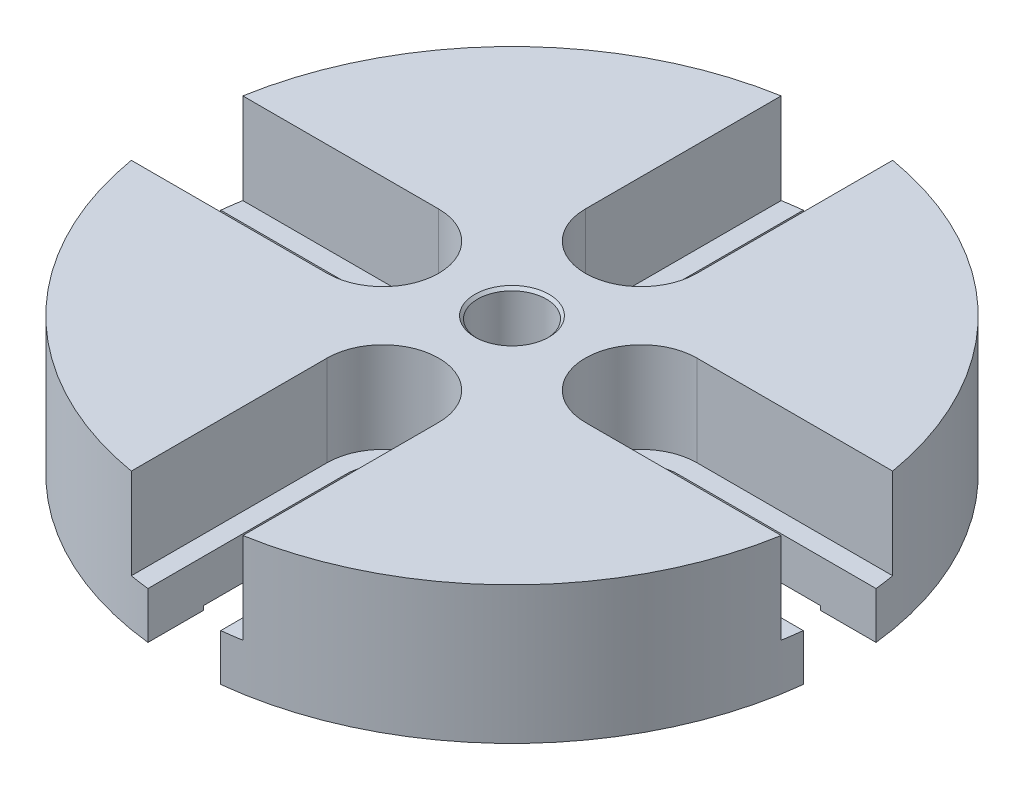
SolidWorks part; units mm, degrees
ref_plane "Front Plane" through (0, 0, 0) normal (0, 0, 1) x (1, 0, 0)
ref_plane "Top Plane" through (0, 0, 0) normal (0, 1, 0) x (1, 0, 0)
ref_plane "Right Plane" through (0, 0, 0) normal (1, 0, 0) x (0, 0, -1)
ref_plane "Plane1" through (0, 0, 0) normal (0, 0, -1) x (-1, 0, 0)
sketch "Sketch1" plane through (0, 0, 0) normal (0, 0, -1) x (-1, 0, 0)
  line L0 (-30.48, -6.35) -> (0, -6.35)
  line L1 (0, -6.35) -> (0, 6.35)
  line L2 (0, 6.35) -> (-30.48, 6.35)
  line L3 (-30.48, 6.35) -> (-30.48, -6.35)
  line L4 (0, -6.35) -> (0, 6.35) construction
revolve "Revolve1" add sketch "Sketch1" angle 360 about L4
sketch "Sketch2" plane through (0, 6.35, 0) normal (0, 1, 0) x (-1, 0, 0)
  line L0 (5.1562, -30.0407) -> (5.1562, -11.938)
  line L1 (-5.1562, -11.938) -> (-5.1562, -30.0407)
  arc A0 (5.1562, -11.938) -> (-5.1562, -11.938) centre (0, -11.938) ccw
  arc A1 (-5.1562, -30.0407) -> (5.1562, -30.0407) centre (0, 0) ccw
extrude "Cut-Extrude1" cut sketch "Sketch2" against normal blind 8.382
sketch "Sketch3" plane through (0, -2.032, 0) normal (0, 1, 0) x (-1, 0, 0)
  line L0 (3.3655, -30.2936) -> (3.3655, -11.938)
  line L1 (-3.3655, -11.938) -> (-3.3655, -30.2936)
  arc A0 (3.3655, -11.938) -> (-3.3655, -11.938) centre (0, -11.938) ccw
  arc A1 (-3.3655, -30.2936) -> (3.3655, -30.2936) centre (0, 0) ccw
extrude "Cut-Extrude2" cut sketch "Sketch3" against normal through all
sketch "Sketch4" plane through (0, 6.35, 0) normal (0, 1, 0) x (-1, 0, 0)
  line L0 (-30.0407, -5.1562) -> (-11.938, -5.1562)
  line L1 (-11.938, 5.1562) -> (-30.0407, 5.1562)
  arc A0 (-11.938, -5.1562) -> (-11.938, 5.1562) centre (-11.938, 0) ccw
  arc A1 (-30.0407, 5.1562) -> (-30.0407, -5.1562) centre (0, 0) ccw
extrude "Cut-Extrude3" cut sketch "Sketch4" against normal blind 8.382
sketch "Sketch5" plane through (0, -2.032, 0) normal (0, 1, 0) x (-1, 0, 0)
  line L0 (-30.2936, -3.3655) -> (-11.938, -3.3655)
  line L1 (-11.938, 3.3655) -> (-30.2936, 3.3655)
  arc A0 (-11.938, -3.3655) -> (-11.938, 3.3655) centre (-11.938, 0) ccw
  arc A1 (-30.2936, 3.3655) -> (-30.2936, -3.3655) centre (0, 0) ccw
extrude "Cut-Extrude4" cut sketch "Sketch5" against normal through all
sketch "Sketch6" plane through (0, 6.35, 0) normal (0, 1, 0) x (-1, 0, 0)
  line L0 (-5.1562, 30.0407) -> (-5.1562, 11.938)
  line L1 (5.1562, 11.938) -> (5.1562, 30.0407)
  arc A0 (-5.1562, 11.938) -> (5.1562, 11.938) centre (0, 11.938) ccw
  arc A1 (5.1562, 30.0407) -> (-5.1562, 30.0407) centre (0, 0) ccw
extrude "Cut-Extrude5" cut sketch "Sketch6" against normal blind 8.382
sketch "Sketch7" plane through (0, -2.032, 0) normal (0, 1, 0) x (-1, 0, 0)
  line L0 (-3.3655, 30.2936) -> (-3.3655, 11.938)
  line L1 (3.3655, 11.938) -> (3.3655, 30.2936)
  arc A0 (-3.3655, 11.938) -> (3.3655, 11.938) centre (0, 11.938) ccw
  arc A1 (3.3655, 30.2936) -> (-3.3655, 30.2936) centre (0, 0) ccw
extrude "Cut-Extrude6" cut sketch "Sketch7" against normal through all
sketch "Sketch8" plane through (0, 6.35, 0) normal (0, 1, 0) x (-1, 0, 0)
  line L0 (30.0407, 5.1562) -> (11.938, 5.1562)
  line L1 (11.938, -5.1562) -> (30.0407, -5.1562)
  arc A0 (11.938, 5.1562) -> (11.938, -5.1562) centre (11.938, 0) ccw
  arc A1 (30.0407, -5.1562) -> (30.0407, 5.1562) centre (0, 0) ccw
extrude "Cut-Extrude7" cut sketch "Sketch8" against normal blind 8.382
sketch "Sketch9" plane through (0, -2.032, 0) normal (0, 1, 0) x (-1, 0, 0)
  line L0 (30.2936, 3.3655) -> (11.938, 3.3655)
  line L1 (11.938, -3.3655) -> (30.2936, -3.3655)
  arc A0 (11.938, 3.3655) -> (11.938, -3.3655) centre (11.938, 0) ccw
  arc A1 (30.2936, -3.3655) -> (30.2936, 3.3655) centre (0, 0) ccw
extrude "Cut-Extrude8" cut sketch "Sketch9" against normal through all
hole_wizard "Hole1" positions "Sketch11" profile "Sketch10" legacy
sketch "Sketch11" plane through (0, -6.35, 0) normal (0, -1, 0) x (-1, 0, 0)
  point P0 (0, 0)
sketch "Sketch10" plane through (0, -6.35, 0) normal (1, 0, 0) x (0, 0, -1)
  line L0 (0, 0) -> (0, 12.7)
  line L1 (0, 12.7) -> (3.175, 12.7)
  line L2 (3.175, 12.7) -> (3.175, 0.381)
  line L3 (3.175, 0.381) -> (25.4, 0.381)
  line L4 (25.4, 0.381) -> (25.4, 0)
  line L5 (25.4, 0) -> (0, 0)
  line L6 (0, 110) -> (0, -10) construction
  dimension "Diameter" = 6.35
  dimension "Depth" = 12.7
  dimension "C-Bore Diameter" = 50.8
  dimension "C-Bore Depth" = 0.381
chamfer "Chamfer1" distance 0.254 angle 45 2 edges at (0, -5.969, -3.175) (0, 6.35, -3.175)
